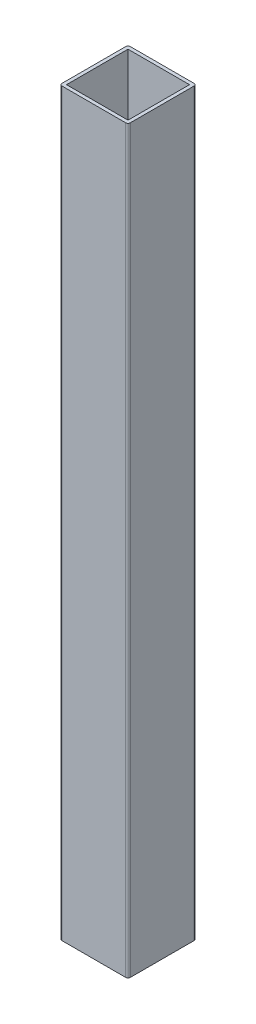
SolidWorks part; units mm, degrees
ref_plane "Front Plane" through (0, 0, 0) normal (0, 0, 1) x (1, 0, 0)
ref_plane "Top Plane" through (0, 0, 0) normal (0, 1, 0) x (1, 0, 0)
ref_plane "Right Plane" through (0, 0, 0) normal (1, 0, 0) x (0, 0, -1)
sketch "Sketch1" plane through (0, 0, 0) normal (0, 1, 0) x (1, 0, 0)
  line L0 (3, 57) -> (57, 57)
  line L1 (2, 0) -> (58, 0)
  line L2 (0, 2) -> (0, 58)
  line L3 (2, 60) -> (58, 60)
  line L4 (60, 2) -> (60, 58)
  line L5 (57, 3) -> (57, 57)
  line L6 (3, 3) -> (57, 3)
  line L7 (3, 3) -> (3, 57)
  arc A0 (58, 60) -> (60, 58) centre (58, 58) cw
  arc A1 (0, 58) -> (2, 60) centre (2, 58) cw
  arc A2 (58, 0) -> (60, 2) centre (58, 2) ccw
  arc A3 (2, 0) -> (0, 2) centre (2, 2) cw
  arc A4 (57, 57) -> (57, 57) centre (57, 57) cw
  arc A5 (57, 3) -> (57, 3) centre (57, 3) ccw
  arc A6 (3, 3) -> (3, 3) centre (3, 3) cw
  arc A7 (3, 57) -> (3, 57) centre (3, 57) cw
  point P9 (0, 60)
  point P14 (0, 0)
  dimension "D2" = 2
  dimension "D3" = 2
  dimension "D1" = 60
  dimension "D4" = 3
extrude "Boss-Extrude1" add sketch "Sketch1" along normal blind 650
